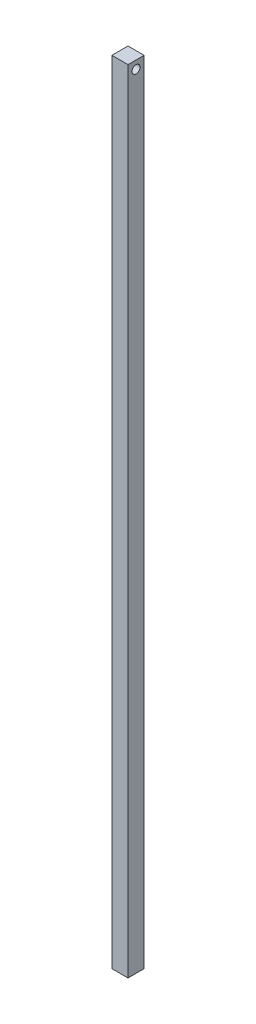
SolidWorks part; units mm, degrees
ref_plane "Front Plane" through (0, 0, 0) normal (0, 0, 1) x (1, 0, 0)
ref_plane "Top Plane" through (0, 0, 0) normal (0, 1, 0) x (1, 0, 0)
ref_plane "Right Plane" through (0, 0, 0) normal (1, 0, 0) x (0, 0, -1)
sketch "Sketch1" plane through (0, 0, 0) normal (0, 1, 0) x (1, 0, 0)
  line L1 (-8.6961, 7.2033) -> (16.7039, 7.2033)
  line L2 (-8.6961, 7.2033) -> (-8.6961, -18.1967)
  line L3 (-8.6961, -18.1967) -> (16.7039, -18.1967)
  line L4 (16.7039, 7.2033) -> (16.7039, -18.1967)
  dimension "D1" = 25.4
  dimension "D2" = 25.4
extrude "Boss-Extrude1" add sketch "Sketch1" along normal blind 1244.6
sketch "Sketch2" plane through (-8.6961, 0, 0) normal (-1, 0, 0) x (0, 0, 1)
  line L0 (18.1967, 1244.6) -> (18.1967, 0) construction
  line L1 (-7.2033, 1244.6) -> (18.1967, 1244.6) construction
  circle A0 centre (5.4967, 1231.9) radius 6.35
  dimension "D1" = 12.7
  dimension "D2" = 12.7
extrude "Cut-Extrude1" cut sketch "Sketch2" against normal blind 25.4
